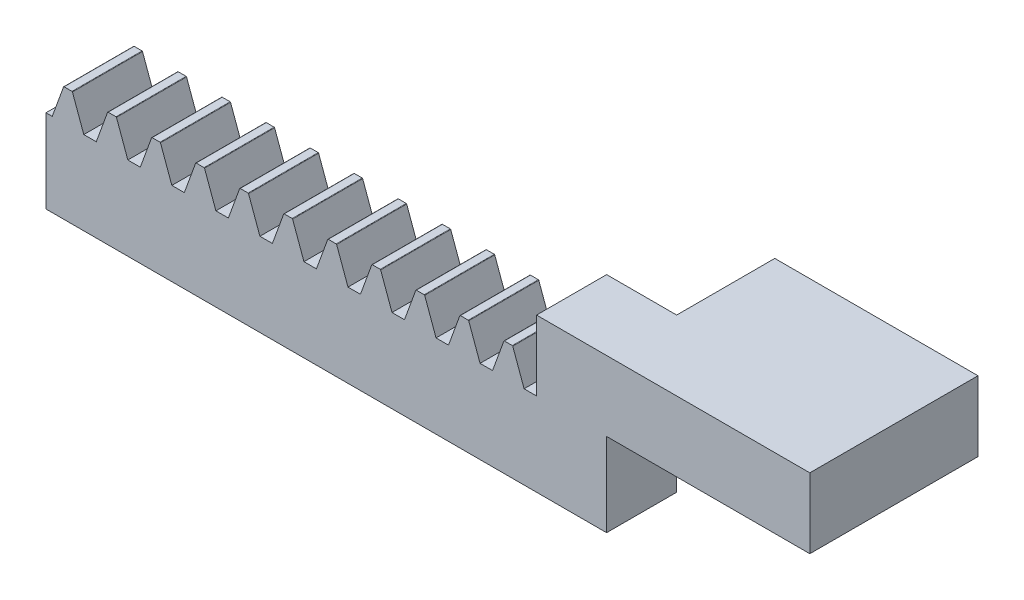
SolidWorks part; units mm, degrees
extrude "Blank" add sketch "BlankSke" against normal blind 5
sketch "BlankSke" plane through (0, 0, 0) normal (0, 0, 1) x (1, 0, 0)
  line L1 (0, 0) -> (40, 0)
  line L2 (0, 0) -> (0, 8.2)
  line L3 (0, 8.2) -> (40, 8.2)
  line L4 (40, 0) -> (40, 8.2)
  dimension "Length" = 40
  dimension "Blank_height" = 8.2
ref_plane "Plane1" through (0, 0, 0) normal (0, 0, 1) x (1, 0, 0)
ref_plane "Plane2" through (0, 0, 0) normal (0, 1, 0) x (1, 0, 0)
ref_plane "Plane3" through (0, 0, 0) normal (1, 0, 0) x (0, 0, -1)
sketch "HoldingSke" plane through (0, 0, 0) normal (0, 1, 0) x (1, 0, 0)
  line L0 (0, 0) -> (0.1392, 0.9903)
  line L1 (-15, 0) -> (100, 0) construction
  line L2 (0, 0) -> (-2.1039, 2.3779)
  line L3 (0, 0) -> (-11.863, 4.5341)
  line L4 (0, 0) -> (8.3795, 2.0892)
  line L5 (0, 0) -> (-23.7986, -8.8762)
  line L6 (0, 0) -> (-10.5278, -7.1032)
  line L9 (-71.009, 38.7566) -> (-33.4213, 52.4374)
  line L10 (-76.2, 3.3779) -> (-69, 3.3779)
  line L11 (0, 0) -> (-5, 0)
  line L12 (-76.2, 101.6) -> (-76.162, 101.6)
  line L13 (24.9733, 27.94) -> (52.9518, 28.4284)
  line L14 (24.9733, 27.94) -> (24.9743, 27.94)
  line L15 (24.9733, 27.94) -> (100.4006, 29.5858)
  circle A0 centre (0, 0) radius 19.05
  circle A1 centre (0, 0) radius 3.6
  circle A2 centre (0, 0) radius 12.7
  dimension "MPH" = 7.2
  dimension "Diameter" = 38.1
  dimension "Num_teeth" = 14
  dimension "Pitch" = 1
  dimension "Show_teeth" = 998
  dimension "Thickness" = 12.7
  dimension "Ap" = 20
  dimension "Pitch_height" = 7.2
  dimension "Width" = 5
  dimension "Backlash" = 0.038
  dimension "Addendum_fac" = 1
  dimension "Dedendum_fac" = 1.25
  dimension "Clearance_fac" = 0.25
  dimension "Dedendum_add" = 0.001
  dimension "Length" = 40
  dimension "Module" = 1
sketch "TooCutSkeIll" plane through (0, 0, 0) normal (0, 0, 1) x (1, 0, 0)
  line L0 (-1.2538, 8.1737) -> (-0.5045, 6.1152)
  line L1 (-0.2687, 5.95) -> (0.2687, 5.95)
  line L2 (0.5045, 6.1152) -> (1.2538, 8.1737)
  line L3 (40, 8.2) -> (0, 8.2) construction
  line L4 (0, 0) -> (0, 64.897) construction
  line L5 (-13.208, 7.2) -> (12.954, 7.2) construction
  line L6 (0, 0) -> (40, 0) construction
  line L7 (0.8994, 7.2) -> (0.8994, 48.7463) construction
  line L8 (-0.8994, 7.2) -> (-0.8994, 48.7463) construction
  line L9 (1.2914, 8.2) -> (1.2914, 8.2254)
  line L10 (-1.2914, 8.2) -> (-1.2914, 8.2254)
  line L11 (-1.2914, 8.2254) -> (1.2914, 8.2254)
  arc A0 (0.2687, 5.95) -> (0.5045, 6.1152) centre (0.2687, 6.201) ccw
  arc A1 (-0.5045, 6.1152) -> (-0.2687, 5.95) centre (-0.2687, 6.201) ccw
  arc A2 (1.2914, 8.2) -> (1.2538, 8.1737) centre (1.2914, 8.16) ccw
  arc A3 (-1.2538, 8.1737) -> (-1.2914, 8.2) centre (-1.2914, 8.16) ccw
  dimension "Pitch_height" = 7.2
  dimension "Addendum_plus" = 1.0254
  dimension "Pressure_angle" = 20
  dimension "Gap_width" = 1.7988
  dimension "Dedendum" = 1.25
extrude "ToothCutIll" cut sketch "TooCutSkeIll" against normal through all
sketch "TooCutSkeSim" plane through (0, 0, 0) normal (0, 0, 1) x (1, 0, 0)
  line L0 (0.4444, 5.95) -> (-0.4444, 5.95)
  line L1 (1.2726, 8.2254) -> (0.4444, 5.95)
  line L2 (0, 17.4625) -> (0, 53.467) construction
  line L3 (1.2726, 8.2254) -> (-1.2726, 8.2254)
  line L6 (-1.2726, 8.2254) -> (-0.4444, 5.95)
  line L9 (-0.8994, 7.2) -> (0.8994, 7.2) construction
  line L10 (0, 0) -> (40, 0) construction
  line L11 (0.8994, 7.2) -> (0.8994, 53.467) construction
  line L12 (-0.8994, 7.2) -> (-0.8994, 53.467) construction
  dimension "Pitch_height" = 7.2
  dimension "Addendum_plus" = 1.0254
  dimension "Pressure_angle" = 20
  dimension "Gap_width" = 1.7988
  dimension "Dedendum" = 1.25
extrude "ToothCutSim" cut sketch "TooCutSkeSim" against normal through all
pattern_linear "TeethCuts" count 13 spacing 3.1416 along (1, 0, 0) of "ToothCutIll", "ToothCutSim"
sketch "Sketch1" plane through (0, 0, 0) normal (0, 0, 1) x (1, 0, 0)
  line L0 (35.002, 5.95) -> (40, 5.95)
  line L1 (40, 0) -> (40, 7.0387) construction
  line L2 (40, 5.95) -> (40, 8.2)
  line L3 (40, 8.2) -> (35.002, 8.2)
  line L4 (35.002, 8.2) -> (35.002, 5.95)
extrude "Boss-Extrude1" add sketch "Sketch1" against normal blind 5
sketch "Sketch3" plane through (0, 0, 0) normal (0, 0, 1) x (1, 0, 0)
  line L1 (35.002, 5.95) -> (40, 5.95)
  line L2 (35.002, 5.95) -> (35.002, 8.2)
  line L3 (35.002, 8.2) -> (40, 8.2)
  line L4 (40, 5.95) -> (40, 8.2)
sketch "Sketch4" plane through (40, 0, 0) normal (1, 0, 0) x (0, 0, -1)
  line L1 (0, 8.2) -> (12, 8.2)
  line L2 (0, 8.2) -> (0, 5.95)
  line L3 (0, 5.95) -> (12, 5.95)
  line L4 (12, 8.2) -> (12, 5.95)
  line L7 (0, 0) -> (0, 8.2) construction
  line L8 (5, 8.2) -> (0, 8.2) construction
  line L9 (0, 0) -> (0, 8.2) construction
  dimension "D1" = 12
  dimension "D2" = 2.25
extrude "Boss-Extrude4" add sketch "Sketch4" along normal blind 14.5
sketch "Sketch6" plane through (0, 8.2, 0) normal (0, 1, 0) x (1, 0, 0)
  line L10 (35.002, 5) -> (35.002, 0)
  line L24 (35.002, 5) -> (35.002, 0)
  line L34 (40, 5) -> (35.002, 5)
  line L35 (40, 5) -> (35.002, 5)
  line L57 (35.002, 0) -> (54.5, 0)
  line L59 (35.002, 0) -> (54.5, 0)
  line L61 (54.5, 0) -> (54.5, 12)
  line L62 (54.5, 0) -> (54.5, 12)
  line L63 (54.5, 12) -> (40, 12)
  line L64 (54.5, 12) -> (40, 12)
  line L65 (40, 12) -> (40, 5)
  line L66 (40, 12) -> (40, 5)
  dimension "D1" = 0
extrude "Boss-Extrude5" add sketch "Sketch6" along normal blind 2.75
ref_plane "Plane4" through (0, 0, -2.5) normal (0, 0, -1) x (-1, 0, 0)
equation "' \"Module@HoldingSke\" = 6.35"
equation "' \"Num_teeth@HoldingSke\" = 12"
equation "' \"Ap@HoldingSke\" =  20"
equation "' \"Ap@HoldingSke\" = 20"
equation "' \"Width@HoldingSke\" = 0.25 * 25.4"
equation "' \"Show_teeth@HoldingSke\" = 500"
equation "' \"Backlash@HoldingSke\" = 0.009 * 25.4"
equation "' \"Addendum_fac@HoldingSke\" = 1.0"
equation "' \"Dedendum_fac@HoldingSke\" = 1.25"
equation "' \"Dedendum_add@HoldingSke\" = 0.00005 * 25.4"
equation "' \"Clearance_fac@HoldingSke\" = 0.25"
equation "' \"Pitch_height@HoldingSke\" = 1 * 25.4"
equation "' \"Length@HoldingSke\" = 4.71 * 25.4"
equation "\"Pitch@HoldingSke\" = 1 / \"Module@HoldingSke\""
equation "\"MPH@HoldingSke\" = \"Dedendum_fac@HoldingSke\" / \"Pitch@HoldingSke\" + 2 * \"Dedendum_add@HoldingSke\" + 0.002 * 25.4"
equation "\"MPH@HoldingSke\" = ((sgn( \"MPH@HoldingSke\" - \"Pitch_height@HoldingSke\")+1)*( \"MPH@HoldingSke\" - \"Pitch_height@HoldingSke\"))/2 + \"Pitch_height@HoldingSke\""
equation "\"Blank_height@BlankSke\" = \"Pitch_height@HoldingSke\" + \"Addendum_fac@HoldingSke\"  / \"Pitch@HoldingSke\" "
equation "\"Length@BlankSke\" =  \"Length@HoldingSke\""
equation "\"Face_width@Blank\" = \"Width@HoldingSke\""
equation "\"Pressure_angle@TooCutSkeIll\" = \"Ap@HoldingSke\""
equation "\"Addendum_plus@TooCutSkeIll\" =  \"Addendum_fac@HoldingSke\"  / \"Pitch@HoldingSke\" + 0.001 *25.4"
equation "\"Dedendum@TooCutSkeIll\" = \"Dedendum_fac@HoldingSke\"  / \"Pitch@HoldingSke\""
equation "\"Pitch_height@TooCutSkeIll\" =  \"MPH@HoldingSke\""
equation "\"Gap_width@TooCutSkeIll\" = 3.14159265 / 2 / \"Pitch@HoldingSke\" + 6 * \"Backlash@HoldingSke\""
equation "\"Pressure_angle@TooCutSkeSim\" = \"Ap@HoldingSke\""
equation "\"Addendum_plus@TooCutSkeSim\" =  \"Addendum_fac@HoldingSke\"  / \"Pitch@HoldingSke\" + 0.001 * 25.4"
equation "\"Dedendum@TooCutSkeSim\" = \"Dedendum_fac@HoldingSke\"  / \"Pitch@HoldingSke\""
equation "\"Pitch_height@TooCutSkeSim\" =  \"MPH@HoldingSke\""
equation "\"Gap_width@TooCutSkeSim\" = 3.14159265 / 2 / \"Pitch@HoldingSke\" + 6 * \"Backlash@HoldingSke\""
equation "\"Root_fillet@TooCutSkeIll\" = \"Clearance_fac@HoldingSke\" / \"Pitch@HoldingSke\" + \"Dedendum_add@HoldingSke\""
equation "\"Break_rad@TooCutSkeIll\" = 0.02 / \"Pitch@HoldingSke\" * 2"
equation "\"Linear_pitch@TeethCuts\" = 3.14159265 / \"Pitch@HoldingSke\""
equation "\"Num_teeth@HoldingSke\" = int( ( \"Length@HoldingSke\" + 0 ) / (3.14159265 / \"Pitch@HoldingSke\")) + 0.9999  + 1"
equation " \"Num_teeth@TeethCuts\" = int( \"Show_teeth@HoldingSke\" ) + 1"
equation " \"Num_teeth@TeethCuts\" = ((sgn( \"Num_teeth@TeethCuts\" - \"Num_teeth@HoldingSke\" )-1)*( \"Num_teeth@TeethCuts\" - \"Num_teeth@HoldingSke\" ))/-2+ \"Num_teeth@HoldingSke\""
equation " \"Num_teeth@TeethCuts\" = ((sgn( \"Num_teeth@TeethCuts\" - 2.0)+1)*( \"Num_teeth@TeethCuts\" - 2.0))/2 +2.0"
